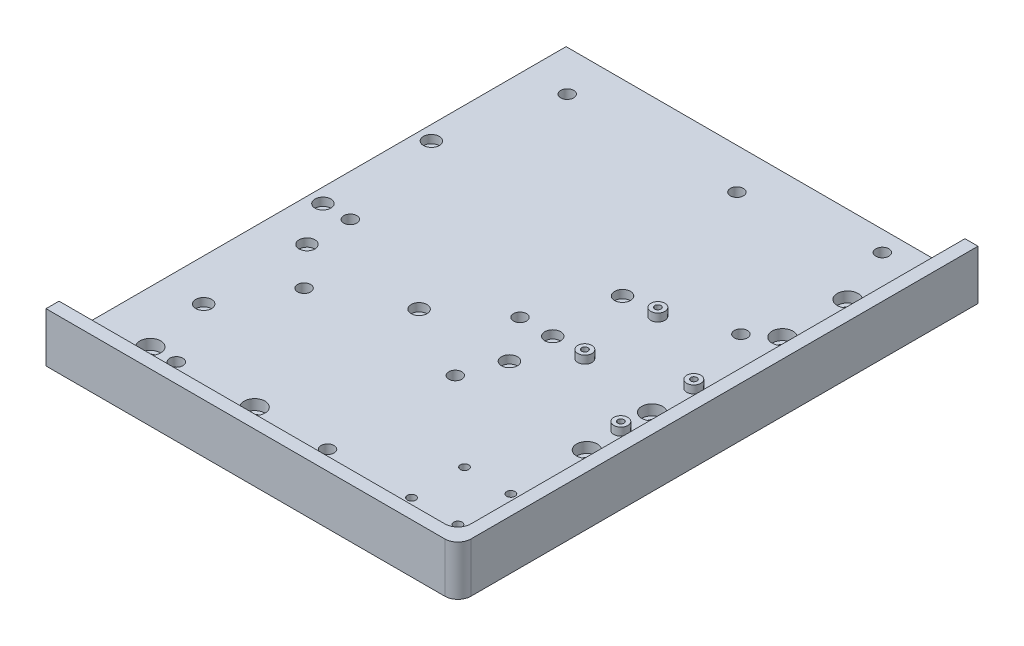
SolidWorks part; units mm, degrees
ref_plane "Front Plane" through (0, 0, 0) normal (0, 0, 1) x (1, 0, 0)
ref_plane "Top Plane" through (0, 0, 0) normal (0, 1, 0) x (1, 0, 0)
ref_plane "Right Plane" through (0, 0, 0) normal (1, 0, 0) x (0, 0, -1)
sketch "Sketch1" plane through (0, 0, 0) normal (0, 1, 0) x (1, 0, 0)
  line L1 (0, 0) -> (158, 0)
  line L2 (0, 0) -> (0, -199.5)
  line L3 (0, -199.5) -> (158, -199.5)
  line L4 (158, 0) -> (158, -199.5)
  dimension "D1" = 158
  dimension "D2" = 199.5
extrude "Boss-Extrude1" add sketch "Sketch1" along normal blind 6.35
sketch "Sketch2" [suppressed] plane through (0, 6.35, 0) normal (0, 1, 0) x (1, 0, 0)
  line L0 (0, -199.5) -> (158, -199.5) construction
  line L1 (158, -199.5) -> (77, -199.5)
  line L2 (158, -199.5) -> (158, -158.5)
  line L3 (158, -158.5) -> (77, -158.5)
  line L4 (77, -199.5) -> (77, -158.5)
  dimension "D1" = 81
  dimension "D2" = 41
sketch "Sketch3" plane through (0, 6.35, 0) normal (0, 1, 0) x (1, 0, 0)
  line L16 (158, -199.5) -> (158, 0) construction
  line L20 (0, -199.5) -> (158, -199.5) construction
  line L21 (158, -199.5) -> (158, 0)
  line L22 (0, -199.5) -> (158, -199.5)
  line L23 (0, -194.5) -> (153, -194.5)
  line L24 (153, -194.5) -> (153, 0)
  line L25 (158, 0) -> (153, 0)
  line L26 (0, -199.5) -> (0, -194.5)
  dimension "D1" = 5
extrude "Boss-Extrude2" add sketch "Sketch3" along normal blind 12.7
sketch "Sketch4" plane through (0, 6.35, 0) normal (0, -1, 0) x (1, 0, 0)
  line L0 (0, 179.5) -> (80, 179.5) construction
  line L1 (0, 0) -> (0, 199.5) construction
  line L3 (0, 199.5) -> (158, 199.5) construction
  line L4 (40, 179.5) -> (40, 188.5903) construction
  line L5 (138, 160) -> (138, 0) construction
  line L7 (158, 0) -> (0, 0) construction
  line L8 (158, 199.5) -> (158, 0) construction
  line L9 (138, 80) -> (152.6176, 80) construction
  point P8 (20, 179.5)
  point P11 (60, 179.5)
  point P20 (138, 130)
  point P21 (138, 105)
  point P22 (138, 30)
  point P23 (138, 80)
  point P24 (138, 55)
  dimension "D1" = 20
  dimension "D2" = 40
  dimension "D3" = 20
  dimension "D4" = 25
  dimension "D5" = 25
  dimension "D6" = 80
  dimension "D7" = 160
hole_wizard "CBORE for M4 SHCS1" positions "Sketch4" profile "Sketch5" counterbore size "M4" standard "ANSI Metric" end condition up to next
sketch "Sketch5" plane through (138, 6.35, 55) normal (1, 0, 0) x (0, 0, 1)
  line L0 (0, 0) -> (0, 6.35)
  line L1 (0, 6.35) -> (2.25, 6.35)
  line L3 (2.25, 6.35) -> (2.25, 4)
  line L4 (2.25, 4) -> (4, 4)
  line L5 (4, 4) -> (4, 0)
  line L7 (4, 0) -> (0, 0)
  line L11 (0, -6.35) -> (0, 107.95) construction
  dimension "Thru Hole Dia." = 4.5
  dimension "Thru Hole Depth" = 6.35
  dimension "C'Bore Dia." = 8
  dimension "C'Bore Depth" = 4
sketch "Sketch7" [suppressed] plane through (0, 0, 0) normal (0, 0, -1) x (-1, 0, 0)
  line L0 (-79, 19.05) -> (-79, 4.7647) construction
  line L1 (-158, 19.05) -> (0, 19.05) construction
  line L2 (-158, 19.05) -> (-158, 0) construction
  line L3 (-129, 19.05) -> (0, 19.05)
  line L4 (-129, 19.05) -> (-129, 9.05)
  line L5 (-129, 9.05) -> (0, 9.05)
  line L6 (0, 19.05) -> (0, 9.05)
  line L7 (0, 19.05) -> (0, 0) construction
  dimension "D2" = 10
  dimension "D3" = 29
extrude "Cut-Extrude2" [suppressed] cut sketch "Sketch7" against normal up to next
fillet "Fillet1" [suppressed] radius 5
fillet "Fillet2" radius 5 1 edges at (158, 9.525, 199.5)
fillet "Fillet3" radius 5 1 edges at (153, 12.7, 194.5)
sketch "Sketch8" plane through (0, 6.35, 0) normal (0, 1, 0) x (1, 0, 0)
  line L2 (153, 0) -> (153, -189.5) construction
  line L3 (153, 0) -> (0, 0) construction
  circle A0 centre (129.05, -62) radius 2.5
  circle A1 centre (129.05, -7.75) radius 2.5
  dimension "D1" = 5
  dimension "D2" = 54.25
  dimension "D3" = 23.95
  dimension "D4" = 7.75
extrude "eStop" cut sketch "Sketch8" against normal through all
sketch "Sketch9" plane through (0, 6.35, 0) normal (0, 1, 0) x (1, 0, 0)
  line L0 (153, 0) -> (0, 0) construction
  line L1 (81.1, -98.77) -> (16, -98.77) construction
  line L2 (81.1, -98.77) -> (81.1, -15.57) construction
  line L3 (81.1, -15.57) -> (16, -15.57) construction
  line L4 (16, -98.77) -> (16, -15.57) construction
  line L5 (81.1, -98.77) -> (16, -15.57) construction
  line L6 (81.1, -15.57) -> (16, -98.77) construction
  line L13 (0, 0) -> (0, -194.5) construction
  circle A0 centre (16, -15.57) radius 2.5
  circle A1 centre (81.1, -15.57) radius 2.5
  circle A2 centre (81.1, -98.77) radius 2.5
  circle A3 centre (16, -98.77) radius 2.5
  point P0 (48.55, -57.17)
  point P23 (138, -30)
  dimension "D5" = 5
  dimension "D7" = 16
  dimension "D1" = 83.2
  dimension "D2" = 65.1
  dimension "D6" = 57.17
extrude "NucleoAndPi" cut sketch "Sketch9" against normal through all
sketch "Sketch10" plane through (0, 6.35, 0) normal (0, 1, 0) x (1, 0, 0)
  line L1 (138, -72) -> (107.2, -72) construction
  line L2 (138, -72) -> (138, -89) construction
  line L3 (138, -89) -> (107.2, -89) construction
  line L4 (107.2, -72) -> (107.2, -89) construction
  line L5 (138, -72) -> (107.2, -89) construction
  line L6 (138, -89) -> (107.2, -72) construction
  circle A0 centre (138, -89) radius 1.2
  circle A1 centre (107.2, -72) radius 1.2
  circle A2 centre (138, -89) radius 2.7
  circle A3 centre (107.2, -72) radius 2.7
  circle A4 centre (129.05, -62) radius 2.5 construction
  point P0 (122.6, -80.5)
  point P18 (138, -55)
  dimension "D3" = 2.4
  dimension "D4" = 1.5
  dimension "D1" = 17
  dimension "D2" = 30.8
  dimension "D5" = 10
extrude "Bucks - Extrude" add sketch "Sketch10" along normal blind 3
sketch "Sketch11" plane through (0, 6.35, 0) normal (0, 1, 0) x (1, 0, 0)
  circle A0 centre (138, -89) radius 1.6
  circle A1 centre (107.2, -72) radius 1.6
  dimension "D1" = 3.2
extrude "Bucks - Cut" cut sketch "Sketch11" against normal up to next (6.35 mm away)
pattern_linear "Buck 2" count 2 spacing 28 along (0, 0, 1) of "Bucks - Extrude", "Bucks - Cut"
sketch "Sketch12" plane through (0, 6.35, 0) normal (0, 1, 0) x (1, 0, 0)
  line L1 (88, -179.5) -> (30, -179.5) construction
  line L2 (88, -179.5) -> (88, -130.5) construction
  line L3 (88, -130.5) -> (30, -130.5) construction
  line L4 (30, -179.5) -> (30, -130.5) construction
  circle A0 centre (30, -130.5) radius 2.5
  circle A1 centre (88, -130.5) radius 2.5
  circle A2 centre (88, -179.5) radius 2.5
  circle A3 centre (30, -179.5) radius 2.5
  point P4 (60, -179.5)
  point P12 (138, -130)
  dimension "D4" = 5
  dimension "D1" = 58
  dimension "D2" = 49
  dimension "D3" = 50
extrude "Pi" cut sketch "Sketch12" against normal through all
sketch "Sketch13" plane through (0, 6.35, 0) normal (0, 1, 0) x (1, 0, 0)
  line L1 (138, -159.18) -> (120.22, -159.18) construction
  line L2 (138, -159.18) -> (138, -179.5) construction
  line L3 (138, -179.5) -> (120.22, -179.5) construction
  line L4 (120.22, -159.18) -> (120.22, -179.5) construction
  circle A0 centre (120.22, -159.18) radius 1.6
  circle A1 centre (120.22, -179.5) radius 1.6
  circle A2 centre (138, -159.18) radius 1.6
  circle A3 centre (138, -179.5) radius 1.6
  point P8 (138, -130)
  point P9 (88, -179.5)
  dimension "D3" = 3.2
  dimension "D1" = 17.78
  dimension "D2" = 20.32
extrude "IMU" cut sketch "Sketch13" against normal through all
sketch "Sketch15" plane through (0, 6.35, 0) normal (0, 1, 0) x (1, 0, 0)
  line L0 (16, -15.57) -> (16, -98.77) construction
  line L1 (0, 0) -> (0, -194.5) construction
  line L3 (30, -130.5) -> (88, -130.5) construction
  line L4 (59, -115.385) -> (93.65, -115.385) construction
  line L5 (93.65, -98.77) -> (93.65, -115.385) construction
  line L6 (107.2, -72) -> (93.65, -72) construction
  line L7 (93.65, -98.77) -> (93.65, -72) construction
  line L8 (30, -130.5) -> (30, -179.5) construction
  circle A1 centre (5.5, -57.17) radius 3.05
  circle A2 centre (5.5, -98.77) radius 3.05
  circle A3 centre (16, -115.385) radius 3.05
  circle A4 centre (59, -115.385) radius 3.05
  circle A5 centre (93.65, -98.77) radius 3.05
  circle A6 centre (93.65, -115.385) radius 3.05
  circle A7 centre (93.65, -72) radius 3.05
  circle A8 centre (16, -155) radius 3.05
  point P1 (16, -57.17)
  point P21 (59, -130.5)
  point P24 (81.1, -98.77)
  point P36 (30, -155)
  dimension "D1" = 6.1
  dimension "D2" = 16.615
  dimension "D3" = 12.55
  dimension "D4" = 5.5
extrude "MAGNETS" cut sketch "Sketch15" against normal blind 3.1
ref_plane "Plane1" through (0, 0, 99.75) normal (0, 0, -1) x (-1, 0, 0)
